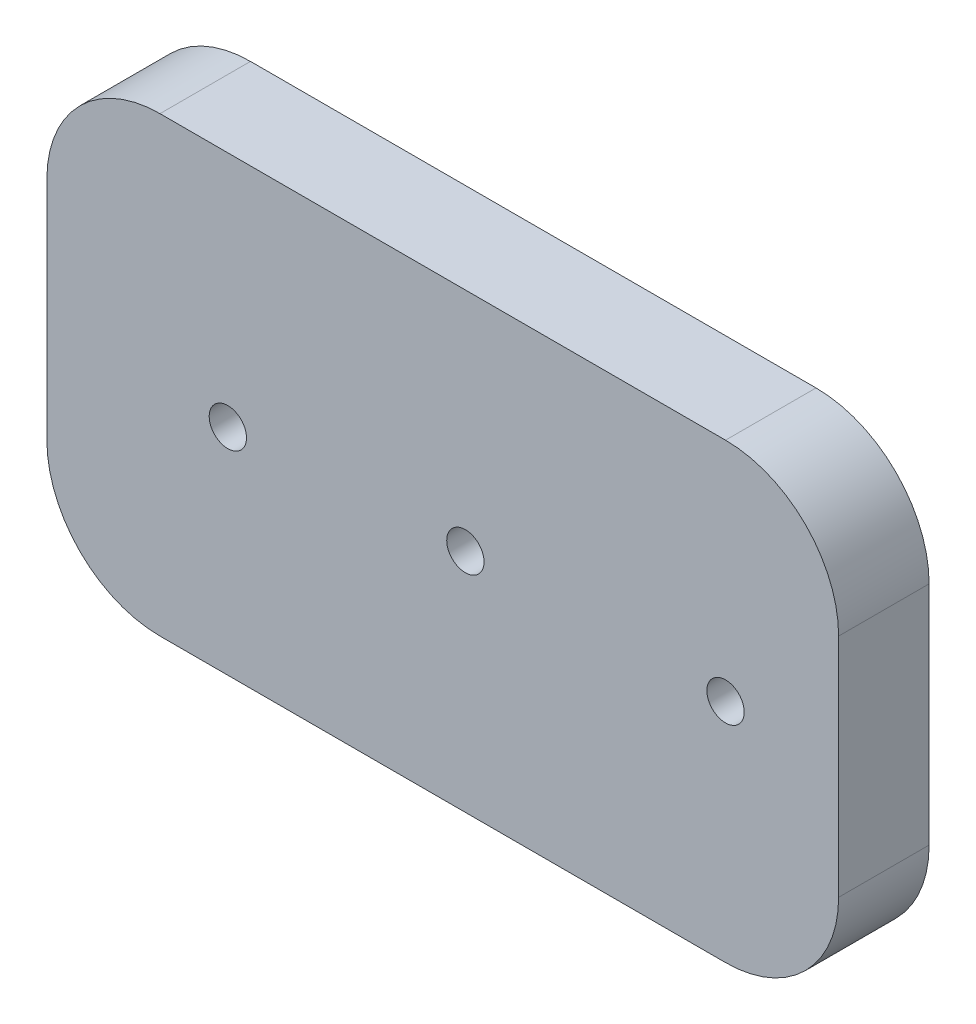
SolidWorks part; units mm, degrees
ref_plane "Front Plane" through (0, 0, 0) normal (0, 0, 1) x (1, 0, 0)
ref_plane "Top Plane" through (0, 0, 0) normal (0, 1, 0) x (1, 0, 0)
ref_plane "Right Plane" through (0, 0, 0) normal (1, 0, 0) x (0, 0, -1)
sketch "Sketch1" plane through (0, 0, 0) normal (0, 0, 1) x (1, 0, 0)
  line L1 (-35, -20) -> (35, -20)
  line L2 (-35, -20) -> (-35, 20)
  line L3 (-35, 20) -> (35, 20)
  line L4 (35, -20) -> (35, 20)
  line L5 (-35, -20) -> (35, 20) construction
  line L6 (-35, 20) -> (35, -20) construction
  point P0 (0, 0)
  dimension "D1" = 40
  dimension "D2" = 70
extrude "Boss-Extrude1" add sketch "Sketch1" along normal blind 10
sketch "Sketch2" plane through (0, 0, 0) normal (0, 0, -1) x (-1, 0, 0)
  circle A0 centre (-25, 0) radius 1.65
  circle A1 centre (-2, 0) radius 1.65
  circle A2 centre (19, -1) radius 1.65
  point P4 (0, 0)
  point P5 (0, 0)
  dimension "D1" = 3.3
  dimension "D4" = 3.3
  dimension "D2" = 23
  dimension "D3" = 2
  dimension "D5" = 1
  dimension "D6" = 21
extrude "Cut-Extrude1" cut sketch "Sketch2" against normal through all
fillet "Fillet1" radius 10 4 edges at (-35, 20, 5) (-35, -20, 5) (35, -20, 5) (35, 20, 5)
shell "Shell2" thickness 1
sketch "Sketch3" plane through (0, 0, 0) normal (0, 0, -1) x (-1, 0, 0)
  circle A1 centre (-2, 0) radius 2.65 construction
  circle A2 centre (-25, 0) radius 2.65 construction
  circle A4 centre (-2, 0) radius 2.65
  circle A5 centre (-25, 0) radius 2.65
  circle A7 centre (-2, 0) radius 1.65 construction
  circle A8 centre (-25, 0) radius 1.65 construction
  circle A10 centre (-2, 0) radius 1.65
  circle A11 centre (-25, 0) radius 1.65
extrude "Boss-Extrude2" add sketch "Sketch3" along normal blind 4
sketch "Sketch4" plane through (0, 0, 0) normal (0, 0, -1) x (-1, 0, 0)
  line L4 (35, -10) -> (35, 10)
  line L5 (25, 20) -> (-25, 20)
  line L6 (-35, 10) -> (-35, -10)
  line L7 (-25, -20) -> (25, -20)
  line L8 (35, -10) -> (35, 10)
  line L9 (25, 20) -> (-25, 20)
  line L10 (-35, 10) -> (-35, -10)
  line L11 (-25, -20) -> (25, -20)
  line L16 (33, -10) -> (33, 10)
  line L17 (25, 18) -> (-25, 18)
  line L18 (-33, 10) -> (-33, -10)
  line L19 (-25, -18) -> (25, -18)
  line L20 (33, -10) -> (33, 10)
  line L21 (25, 18) -> (-25, 18)
  line L22 (-33, 10) -> (-33, -10)
  line L23 (-25, -18) -> (25, -18)
  arc A4 (35, 10) -> (25, 20) centre (25, 10) ccw
  arc A5 (-25, 20) -> (-35, 10) centre (-25, 10) ccw
  arc A6 (-35, -10) -> (-25, -20) centre (-25, -10) ccw
  arc A7 (25, -20) -> (35, -10) centre (25, -10) ccw
  arc A8 (35, 10) -> (25, 20) centre (25, 10) ccw
  arc A9 (-25, 20) -> (-35, 10) centre (-25, 10) ccw
  arc A10 (-35, -10) -> (-25, -20) centre (-25, -10) ccw
  arc A11 (25, -20) -> (35, -10) centre (25, -10) ccw
  arc A16 (33, 10) -> (25, 18) centre (25, 10) ccw
  arc A17 (-25, 18) -> (-33, 10) centre (-25, 10) ccw
  arc A18 (-33, -10) -> (-25, -18) centre (-25, -10) ccw
  arc A19 (25, -18) -> (33, -10) centre (25, -10) ccw
  arc A20 (33, 10) -> (25, 18) centre (25, 10) ccw
  arc A21 (-25, 18) -> (-33, 10) centre (-25, 10) ccw
  arc A22 (-33, -10) -> (-25, -18) centre (-25, -10) ccw
  arc A23 (25, -18) -> (33, -10) centre (25, -10) ccw
  dimension "D1" = 0
  dimension "D2" = 2
extrude "Cut-Extrude2" cut sketch "Sketch4" against normal blind 2
